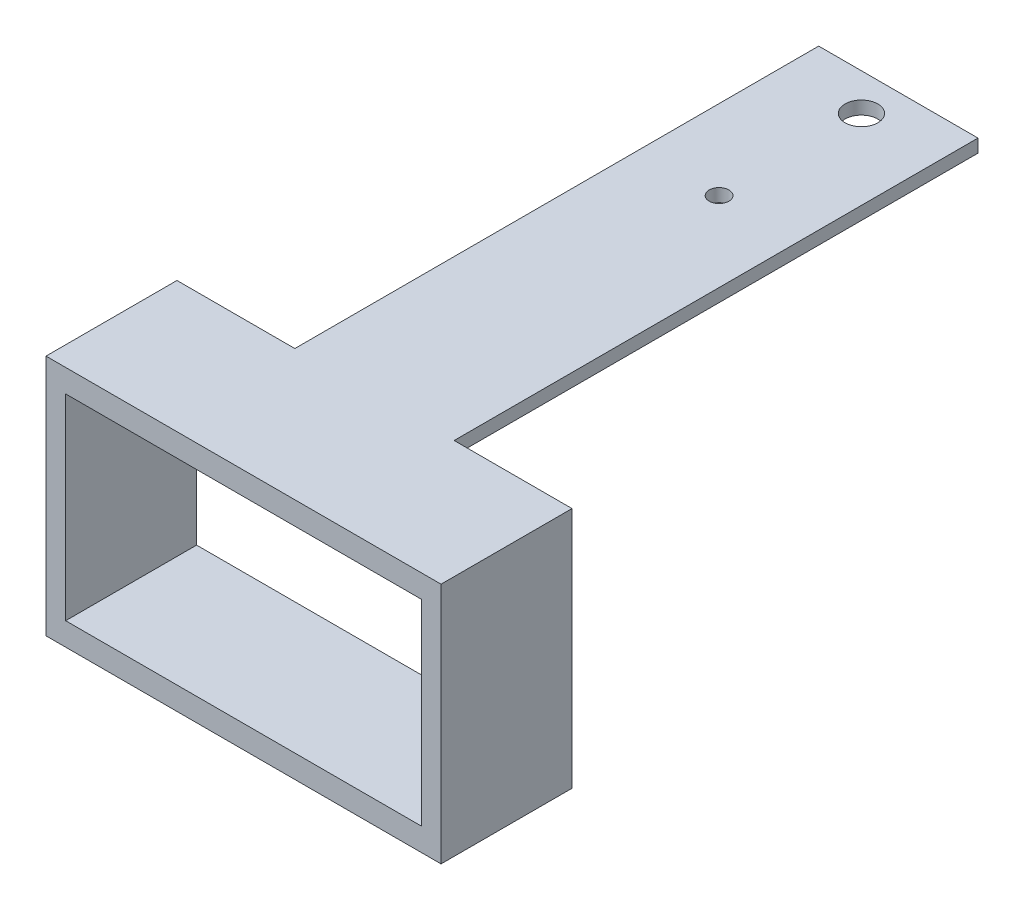
SolidWorks part; units mm, degrees
ref_plane "Front Plane" through (0, 0, 0) normal (0, 0, 1) x (1, 0, 0)
ref_plane "Top Plane" through (0, 0, 0) normal (0, 1, 0) x (1, 0, 0)
ref_plane "Right Plane" through (0, 0, 0) normal (1, 0, 0) x (0, 0, -1)
sketch "Sketch2" plane through (0, 0, 0) normal (0, 1, 0) x (1, 0, 0)
  line L0 (-7.9412, 23.5294) -> (16.3888, 23.5294)
  line L1 (16.3888, 23.5294) -> (16.3888, -36.4706)
  line L2 (16.3888, -36.4706) -> (34.3888, -36.4706)
  line L3 (34.3888, -36.4706) -> (34.3888, -56.4706)
  line L4 (34.3888, -56.4706) -> (-25.9412, -56.4706)
  line L5 (-25.9412, -56.4706) -> (-25.9412, -36.4706)
  line L6 (-25.9412, -36.4706) -> (-7.9412, -36.4706)
  line L7 (-7.9412, -36.4706) -> (-7.9412, 23.5294)
  dimension "D1" = 24.33
  dimension "D2" = 18
  dimension "D3" = 18
  dimension "D4" = 20
  dimension "D5" = 60
extrude "Boss-Extrude1" add sketch "Sketch2" along normal blind 2
sketch "Sketch3" plane through (0, 0, 0) normal (0, -1, 0) x (-1, 0, 0)
  line L0 (25.9412, -36.4706) -> (25.9412, -56.4706) construction
  line L1 (25.9412, -56.4706) -> (-34.3888, -56.4706)
  line L2 (25.9412, -56.4706) -> (25.9412, -36.4706)
  line L3 (25.9412, -36.4706) -> (-34.3888, -36.4706)
  line L4 (-34.3888, -56.4706) -> (-34.3888, -36.4706)
  line L5 (-34.3888, -56.4706) -> (-34.3888, -36.4706) construction
  line L6 (25.9412, -56.4706) -> (-34.3888, -56.4706) construction
  line L7 (7.9412, -36.4706) -> (25.9412, -36.4706) construction
extrude "Boss-Extrude2" add sketch "Sketch3" along normal blind 30
sketch "Sketch4" plane through (0, 0, 36.4706) normal (0, 0, -1) x (-1, 0, 0)
  line L0 (25.9412, 2) -> (25.9412, -30) construction
  line L1 (22.9412, -28.5) -> (-31.3888, -28.5)
  line L2 (22.9412, -28.5) -> (22.9412, -1.5)
  line L3 (22.9412, -1.5) -> (-31.3888, -1.5)
  line L4 (-31.3888, -28.5) -> (-31.3888, -1.5)
  line L5 (-34.3888, 2) -> (-34.3888, -30) construction
  line L6 (25.9412, -30) -> (-34.3888, -30) construction
  line L7 (7.9412, 0) -> (-16.3888, 0) construction
  dimension "D1" = 3
  dimension "D2" = 3
  dimension "D3" = 1.5
  dimension "D4" = 1.5
extrude "Cut-Extrude1" cut sketch "Sketch4" against normal blind 20
sketch "Sketch5" plane through (0, 0, 0) normal (0, -1, 0) x (-1, 0, 0)
  line L0 (-16.3888, -36.4706) -> (-16.3888, 23.5294) construction
  circle A0 centre (-4.2238, 16.1506) radius 1.5
  dimension "D2" = 3
  dimension "D1" = 12.165
extrude "Cut-Extrude2" cut sketch "Sketch5" against normal blind 2
sketch "Sketch6" plane through (0, -30, 0) normal (0, -1, 0) x (1, 0, 0)
  line L0 (34.3888, 56.4706) -> (-25.9412, 56.4706) construction
  line L1 (-25.9412, 56.4706) -> (34.3888, 56.4706)
  line L2 (-25.9412, 56.4706) -> (-25.9412, 36.4706)
  line L3 (-25.9412, 36.4706) -> (34.3888, 36.4706)
  line L4 (34.3888, 56.4706) -> (34.3888, 36.4706)
  line L5 (-25.9412, 56.4706) -> (-25.9412, 36.4706) construction
  line L6 (34.3888, 36.4706) -> (34.3888, 56.4706) construction
  line L7 (-25.9412, 36.4706) -> (34.3888, 36.4706) construction
extrude "Boss-Extrude3" add sketch "Sketch6" along normal blind 5
sketch "Sketch8" plane through (0, -28.5, 0) normal (0, 1, 0) x (1, 0, 0)
  line L0 (31.3888, -56.4706) -> (-22.9412, -56.4706) construction
  line L1 (31.3888, -36.4706) -> (-22.9412, -36.4706)
  line L2 (31.3888, -36.4706) -> (31.3888, -56.4706)
  line L3 (31.3888, -56.4706) -> (-22.9412, -56.4706)
  line L4 (-22.9412, -36.4706) -> (-22.9412, -56.4706)
  line L5 (31.3888, -56.4706) -> (31.3888, -36.4706) construction
  line L6 (31.3888, -36.4706) -> (-22.9412, -36.4706) construction
  line L7 (-22.9412, -56.4706) -> (-22.9412, -36.4706) construction
extrude "Cut-Extrude3" cut sketch "Sketch8" against normal blind 3
sketch "Sketch9" plane through (0, 2, 0) normal (0, 1, 0) x (1, 0, 0)
  line L0 (16.3888, 23.5294) -> (-7.9412, 23.5294) construction
  line L1 (-7.9412, 43.5294) -> (16.3888, 43.5294)
  line L2 (-7.9412, 43.5294) -> (-7.9412, 23.5294)
  line L3 (-7.9412, 23.5294) -> (16.3888, 23.5294)
  line L4 (16.3888, 43.5294) -> (16.3888, 23.5294)
  line L5 (-7.9412, 23.5294) -> (-7.9412, -36.4706) construction
  line L6 (16.3888, -36.4706) -> (16.3888, 23.5294) construction
  dimension "D1" = 20
extrude "Boss-Extrude4" add sketch "Sketch9" against normal blind 2
sketch "Sketch10" plane through (0, 0, 0) normal (0, -1, 0) x (-1, 0, 0)
  line L0 (7.9412, 43.5294) -> (7.9412, -36.4706) construction
  circle A0 centre (-4.2238, 37.8934) radius 2.5
  dimension "D1" = 5
  dimension "D2" = 12.165
extrude "Cut-Extrude4" cut sketch "Sketch10" against normal blind 2
